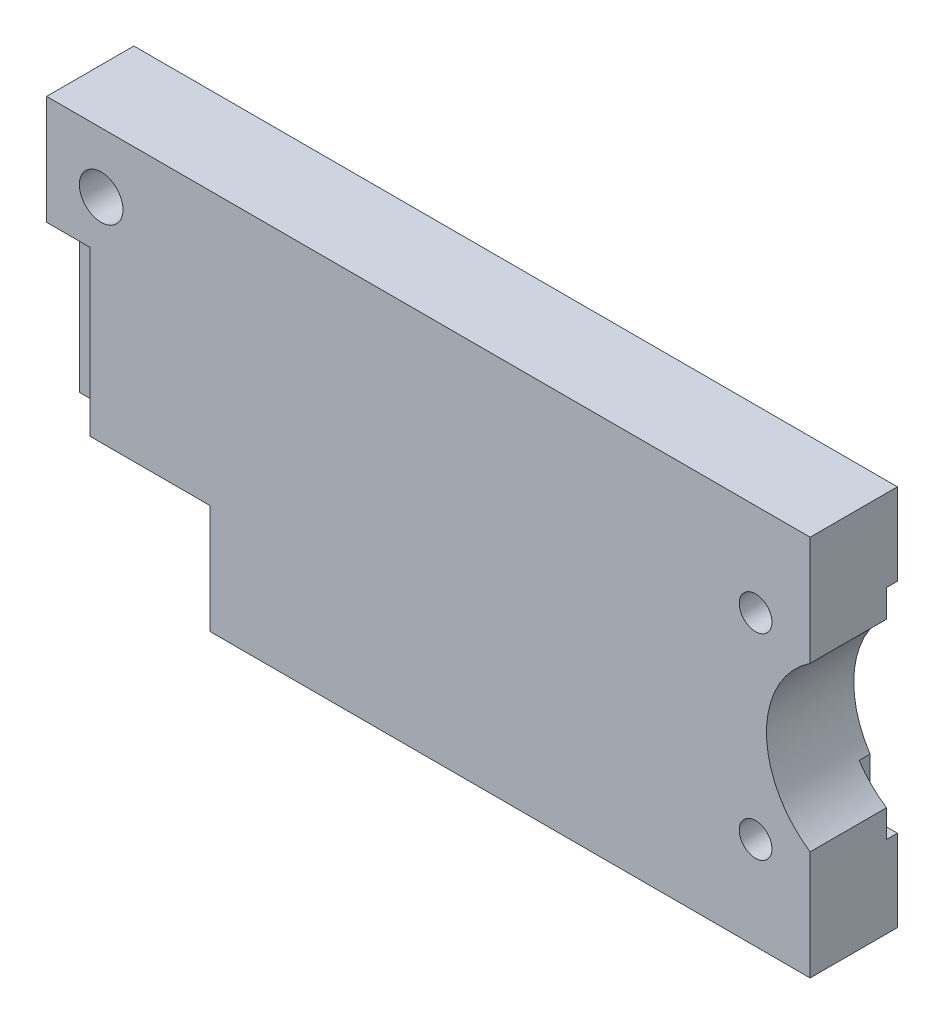
SolidWorks part; units mm, degrees
ref_plane "Front Plane" through (0, 0, 0) normal (0, 0, 1) x (1, 0, 0)
ref_plane "Top Plane" through (0, 0, 0) normal (0, 1, 0) x (1, 0, 0)
ref_plane "Right Plane" through (0, 0, 0) normal (1, 0, 0) x (0, 0, -1)
sketch "Sketch1" plane through (0, 0, 0) normal (0, 0, 1) x (1, 0, 0)
  line L0 (35, -17.5) -> (-35, -17.5)
  line L1 (-35, -17.5) -> (-35, 17.5)
  line L2 (-35, 17.5) -> (35, 17.5)
  line L3 (35, 17.5) -> (35, -17.5)
  line L4 (-35, -7.5) -> (-20, -7.5)
  line L5 (-20, -7.5) -> (-20, -17.5)
  line L6 (30, 9) -> (30, -9)
  circle A0 centre (-30, 12) radius 2
  circle A1 centre (30, 9) radius 1.5
  circle A2 centre (30, -9) radius 1.5
  point P2 (0, -17.5)
  point P5 (-35, 0)
  point P16 (30, 0)
  point P17 (35, 0)
  dimension "D5" = 4
  dimension "D6" = 3
  dimension "D9" = 5
  dimension "D10" = 3
  dimension "D1" = 70
  dimension "D2" = 35
  dimension "D3" = 55
  dimension "D4" = 10
  dimension "D7" = 18
  dimension "D8" = 60
extrude "Boss-Extrude1" add sketch "Sketch1" along normal mid plane 8
sketch "Sketch2" plane through (0, 0, 4) normal (0, 0, 1) x (1, 0, 0)
  line L0 (-35, 7.5) -> (-35, -7.5)
  line L3 (-35, -7.5) -> (-35, 17.5) construction
  line L4 (35, 17.5) -> (35, -17.5) construction
  line L5 (-35, -7.5) -> (-31, -7.5)
  line L6 (-35, -7.5) -> (-20, -7.5) construction
  line L7 (-35, 7.5) -> (-31, 7.5)
  line L8 (-31, 7.5) -> (-31, -7.5)
  point P5 (-35, 0)
  point P8 (35, 0)
  dimension "D1" = 15
  dimension "D2" = 4
extrude "Cut-Extrude1" cut sketch "Sketch2" against normal blind 3 contours L8 L5 L0 L7
sketch "Sketch3" plane through (0, 0, -4) normal (0, 0, -1) x (-1, 0, 0)
  line L0 (-35, 10) -> (-35, -10)
  line L1 (-35, 17.5) -> (-35, -17.5) construction
  line L2 (-35, -10) -> (-32.5, -10)
  line L3 (-32.5, -10) -> (-32.5, 10)
  line L4 (-32.5, 10) -> (-35, 10)
  point P4 (-35, 0)
  point P7 (-35, 0)
  dimension "D1" = 2.5
  dimension "D2" = 20
extrude "Cut-Extrude2" cut sketch "Sketch3" against normal blind 1
sketch "Sketch5" plane through (0, 0, 4) normal (0, 0, 1) x (1, 0, 0)
  line L0 (35, 0) -> (40, 0)
  line L1 (35, 17.5) -> (35, -17.5) construction
  line L2 (35, 17.5) -> (35, -17.5)
  line L3 (35, -17.5) -> (-20, -17.5) construction
  circle A0 centre (40, 0) radius 9
  dimension "D2" = 18
  dimension "D1" = 5
extrude "Cut-Extrude3" cut sketch "Sketch5" against normal up to next
